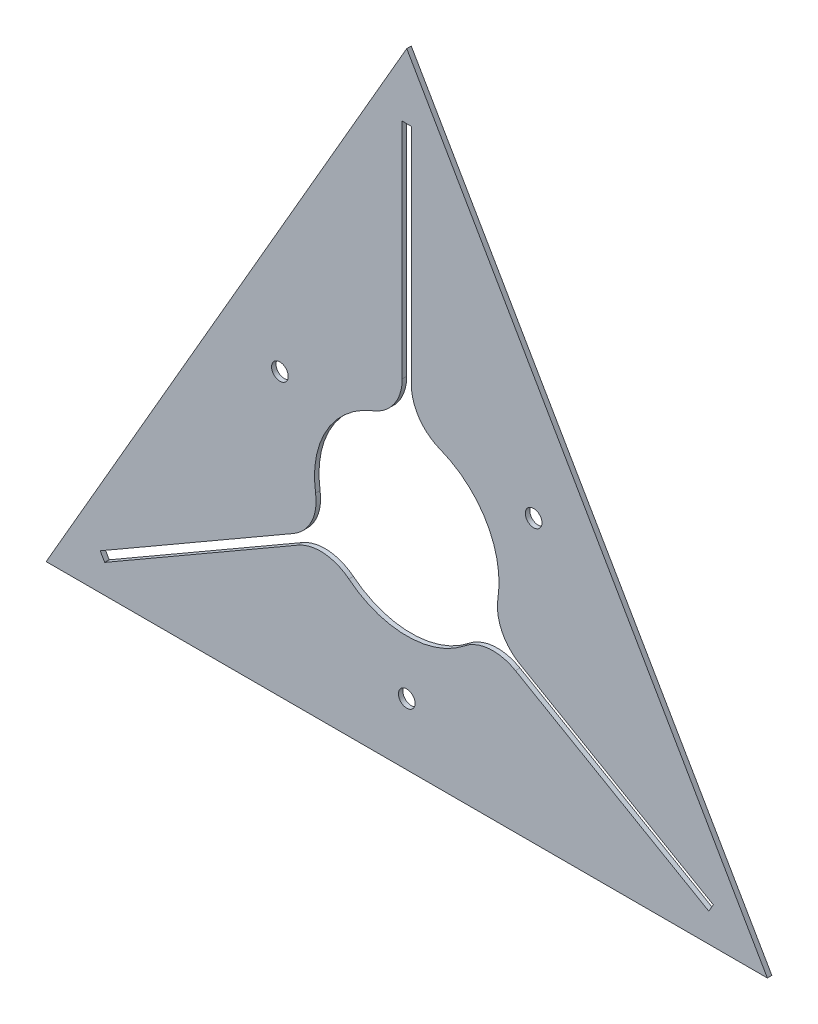
SolidWorks part; units mm, degrees
ref_plane "Front Plane" through (0, 0, 0) normal (0, 0, 1) x (1, 0, 0)
ref_plane "Top Plane" through (0, 0, 0) normal (0, 1, 0) x (1, 0, 0)
ref_plane "Right Plane" through (0, 0, 0) normal (1, 0, 0) x (0, 0, -1)
sketch "Sketch1" plane through (0, 0, 0) normal (0, 0, 1) x (1, 0, 0)
  line L0 (-2.54, 72.1881) -> (-2.54, 197.9944)
  line L1 (0, 234.6351) -> (-203.2, -117.3176)
  line L2 (-203.2, -117.3176) -> (203.2, -117.3176)
  line L3 (203.2, -117.3176) -> (0, 234.6351)
  line L4 (2.54, 72.1881) -> (2.54, 197.9944)
  line L5 (-2.54, 197.9944) -> (2.54, 197.9944)
  line L6 (-2.54, 72.1881) -> (-2.54, 51.9444) construction
  line L7 (0, 0) -> (0, 234.6351) construction
  line L8 (63.7867, -33.8943) -> (172.7382, -96.7975)
  line L9 (61.2467, -38.2938) -> (170.1982, -101.1969)
  line L10 (172.7382, -96.7975) -> (170.1982, -101.1969)
  line L11 (-61.2467, -38.2938) -> (-170.1982, -101.1969)
  line L12 (-63.7867, -33.8943) -> (-172.7382, -96.7975)
  line L13 (-170.1982, -101.1969) -> (-172.7382, -96.7975)
  line L14 (0, 0) -> (0, -117.3176) construction
  circle A1 centre (0, 0) radius 117.3176 construction
  arc A6 (-18.7718, 48.5005) -> (-51.3885, -7.9933) centre (0, 0) ccw
  arc A7 (-18.7718, 48.5005) -> (-2.54, 72.1881) centre (-27.94, 72.1881) ccw
  arc A8 (2.54, 72.1881) -> (18.7718, 48.5005) centre (27.94, 72.1881) ccw
  arc A9 (-2.54, 51.9444) -> (-10.16, 51.0044) centre (0, 0) ccw construction
  arc A10 (61.2467, -38.2938) -> (32.6167, -40.5071) centre (48.5467, -60.2908) ccw
  arc A11 (51.3885, -7.9933) -> (63.7867, -33.8943) centre (76.4867, -11.8973) ccw
  arc A12 (-63.7867, -33.8943) -> (-51.3885, -7.9933) centre (-76.4867, -11.8973) ccw
  arc A13 (-32.6167, -40.5071) -> (-61.2467, -38.2938) centre (-48.5467, -60.2908) ccw
  arc A14 (-32.6167, -40.5071) -> (32.6167, -40.5071) centre (0, 0) ccw
  arc A15 (51.3885, -7.9933) -> (18.7718, 48.5005) centre (0, 0) ccw
  circle A16 centre (0, -82.55) radius 4.699
  circle A17 centre (-71.4904, 41.275) radius 4.699
  circle A18 centre (71.4904, 41.275) radius 4.699
  point P3 (0, 197.9944)
  point P15 (-18.7718, 48.5005)
  point P16 (-2.54, 72.1881)
  point P17 (2.54, 72.1881)
  point P18 (18.7718, 48.5005)
  point P22 (0, 0)
  point P41 (0, 0)
  point P47 (0, 0)
  dimension "D3" = 104.013
  dimension "D6" = 3
  dimension "D5" = 25.4
  dimension "D7" = 7.62
  dimension "D8" = 3
  dimension "D9" = 9.398
  dimension "D1" = 146.05
  dimension "D2" = 5.08
  dimension "D4" = 406.4
  dimension "D10" = 82.55
  dimension "D11" = 82.55
  dimension "D12" = 82.55
extrude "Boss-Extrude1" add sketch "Sketch1" along normal blind 2.54
